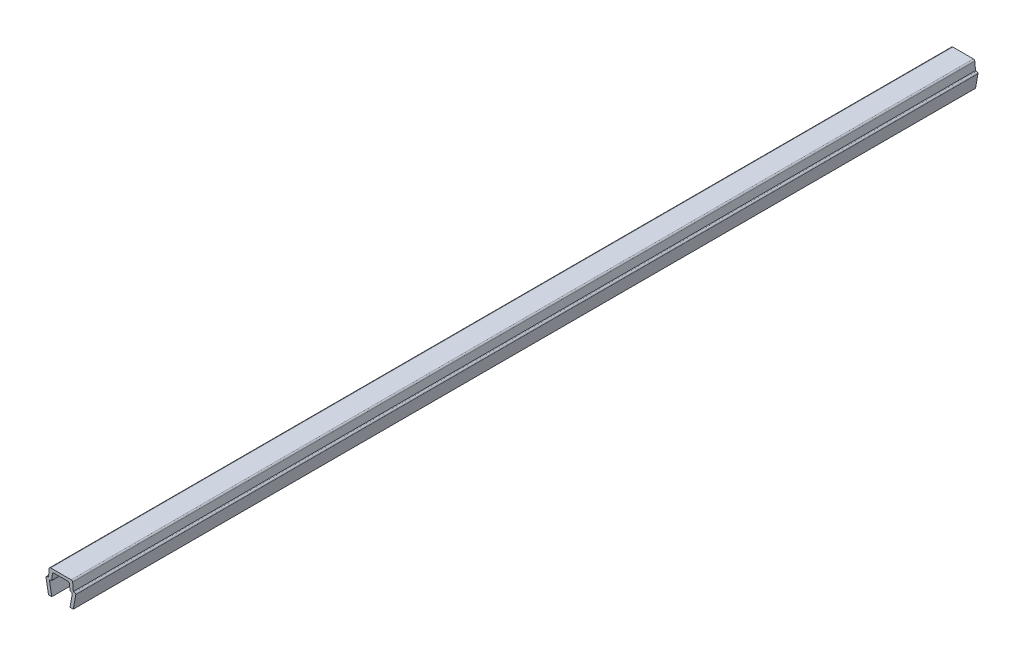
SolidWorks part; units mm, degrees
ref_plane "Front Plane" through (0, 0, 0) normal (0, 0, 1) x (1, 0, 0)
ref_plane "Top Plane" through (0, 0, 0) normal (0, 1, 0) x (1, 0, 0)
ref_plane "Right Plane" through (0, 0, 0) normal (1, 0, 0) x (0, 0, -1)
ref_plane "Plane1" through (0, 0, 0) normal (0, 0, 1) x (1, 0, 0)
sketch "Sketch1" plane through (0, 0, 0) normal (0, 0, 1) x (1, 0, 0)
  line L0 (-3.6, 3.35) -> (-3, 0)
  line L1 (-3, 0) -> (-2.2, 0)
  line L2 (-2.2, 0) -> (-2.7352, 2.9883)
  line L3 (-2.3907, 3.4) -> (-2.2, 3.4)
  line L4 (-2.2, 3.4) -> (-2.0705, 4.8805)
  line L5 (-1.7218, 5.2) -> (1.7218, 5.2)
  line L6 (2.0705, 4.8805) -> (2.2, 3.4)
  line L7 (2.2, 3.4) -> (2.3907, 3.4)
  line L8 (2.7352, 2.9883) -> (2.2, 0)
  line L9 (2.2, 0) -> (3, 0)
  line L10 (3, 0) -> (3.6, 3.35)
  line L11 (3.25, 3.7) -> (3, 3.7)
  line L12 (3, 3.7) -> (2.8355, 5.5805)
  line L13 (2.4868, 5.9) -> (-2.4868, 5.9)
  line L14 (-2.8355, 5.5805) -> (-3, 3.7)
  line L15 (-3, 3.7) -> (-3.25, 3.7)
  arc A0 (-2.7352, 2.9883) -> (-2.3907, 3.4) centre (-2.3907, 3.05) cw
  arc A1 (-2.0705, 4.8805) -> (-1.7218, 5.2) centre (-1.7218, 4.85) cw
  arc A2 (1.7218, 5.2) -> (2.0705, 4.8805) centre (1.7218, 4.85) cw
  arc A3 (2.3907, 3.4) -> (2.7352, 2.9883) centre (2.3907, 3.05) cw
  arc A4 (3.6, 3.35) -> (3.25, 3.7) centre (3.25, 3.35) ccw
  arc A5 (2.8355, 5.5805) -> (2.4868, 5.9) centre (2.4868, 5.55) ccw
  arc A6 (-2.4868, 5.9) -> (-2.8355, 5.5805) centre (-2.4868, 5.55) ccw
  arc A7 (-3.25, 3.7) -> (-3.6, 3.35) centre (-3.25, 3.35) ccw
extrude "Boss-Extrude1" add sketch "Sketch1" against normal mid plane 218
